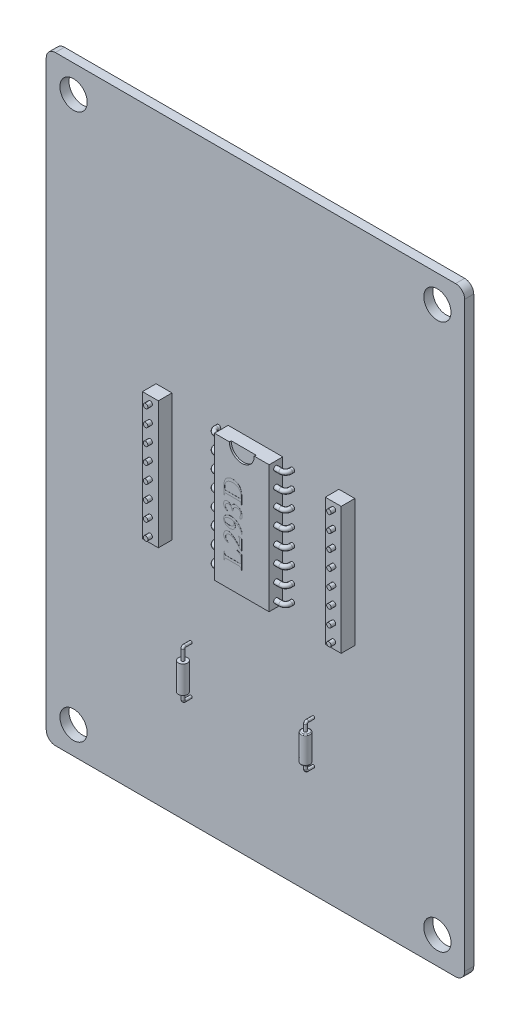
SolidWorks part; units mm, degrees
ref_plane "Plan de face" through (0, 0, 0) normal (0, 0, 1) x (1, 0, 0)
ref_plane "Plan de dessus" through (0, 0, 0) normal (0, 1, 0) x (1, 0, 0)
ref_plane "Plan de droite" through (0, 0, 0) normal (1, 0, 0) x (0, 0, -1)
sketch "Esquisse1" plane through (0, 0, 0) normal (0, 0, 1) x (1, 0, 0)
  line L6 (-23, 33) -> (-23, -33)
  line L7 (-23, -33) -> (23, -33)
  line L8 (23, 33) -> (23, -33)
  line L9 (-23, 33) -> (23, 33)
  circle A0 centre (-20, 30) radius 1.5
  circle A1 centre (20, 30) radius 1.5
  circle A2 centre (20, -30) radius 1.5
  circle A3 centre (-20, -30) radius 1.5
extrude "Boss.-Extru.1" add sketch "Esquisse1" along normal blind 1
fillet "Congé1" radius 1 4 edges at (23, -33, 0.5) (23, 33, 0.5) (-23, 33, 0.5) (-23, -33, 0.5)
sketch "Esquisse2" plane through (0, 0, 1) normal (0, 0, 1) x (1, 0, 0)
  line L2 (-3, 7) -> (3, 7)
  line L3 (3, 7) -> (3, -7)
  line L4 (-3, 7) -> (-3, -7)
  line L5 (-3, -7) -> (3, -7)
extrude "Boss.-Extru.2" add sketch "Esquisse2" along normal blind 1.5
sketch "Esquisse3" plane through (3, 0, 0) normal (1, 0, 0) x (0, 0, -1)
  circle A0 centre (-1.75, 0.9) radius 0.25
  dimension "D1" = 0.5
sketch3d "Esquisse3D1"
  line L0 (3, 0.9, 1.75) -> (3.5632, 0.9, 1.75)
  line L1 (4.0632, 0.9, 1.25) -> (4.0632, 0.9, 0.6073)
  arc A0 (3.5632, 0.9, 1.75) -> (4.0632, 0.9, 1.25) centre (3.5632, 0.9, 1.25) ccw
  point P7 (4.0632, 0.9, 1.75)
  point P8 (3.5632, 1.4, 1.25)
  dimension "D1" = 0.5
sweep "Balayage1" add profiles "Esquisse3" path "Esquisse3D1"
pattern_linear "Répétition linéaire1" count 4 spacing 1.8 along (0, 1, 0) of "Balayage1"
mirror "Symétrie1" about plane through (0, 0, 0) normal (0, 1, 0) of "Répétition linéaire1", "Balayage1"
mirror "Symétrie2" about plane through (0, 0, 0) normal (1, 0, 0) of "Symétrie1", "Balayage1", "Répétition linéaire1"
sketch "Esquisse4" plane through (0, 0, 2.5) normal (0, 0, 1) x (1, 0, 0)
  line L0 (3, 7) -> (-3, 7) construction
  line L1 (-1.3668, 7) -> (1.3668, 7)
  arc A0 (-1.3668, 7) -> (1.3668, 7) centre (0, 7) ccw
extrude "Enlèv. mat.-Extru.1" cut sketch "Esquisse4" against normal blind 0.2
sketch "Esquisse7" plane through (0, 0, 2.5) normal (0, 0, 1) x (1, 0, 0)
  line L0 (0, 20.7797) -> (0, -18.942) construction
  line L1 (-9.1755, 7) -> (-10.9232, 7)
  line L2 (-9.1755, 7) -> (-9.1755, -7)
  line L3 (-9.1755, -7) -> (-10.9232, -7)
  line L4 (-10.9232, 7) -> (-10.9232, -7)
  line L6 (10.9232, 7) -> (10.9232, -7)
  line L7 (9.1755, -7) -> (10.9232, -7)
  line L8 (9.1755, 7) -> (9.1755, -7)
  line L9 (9.1755, 7) -> (10.9232, 7)
extrude "Boss.-Extru.6" add sketch "Esquisse7" against normal blind 1.5 separate body
sketch "Esquisse8" plane through (0, 0, 1) normal (0, 0, -1) x (-1, 0, 0)
  line L0 (0, 14.1831) -> (0, -11.9135) construction
  circle A0 centre (-10.0843, 0.9) radius 0.25
  circle A1 centre (-10.0806, 2.7) radius 0.25
  circle A2 centre (-10.077, 4.5) radius 0.25
  circle A3 centre (-10.0733, 6.3) radius 0.25
  circle A4 centre (-10.0733, -6.3) radius 0.25
  circle A5 centre (-10.077, -4.5) radius 0.25
  circle A6 centre (-10.0806, -2.7) radius 0.25
  circle A7 centre (-10.0843, -0.9) radius 0.25
  circle A8 centre (10.0843, -0.9) radius 0.25
  circle A9 centre (10.0806, -2.7) radius 0.25
  circle A10 centre (10.077, -4.5) radius 0.25
  circle A11 centre (10.0733, -6.3) radius 0.25
  circle A12 centre (10.0733, 6.3) radius 0.25
  circle A13 centre (10.077, 4.5) radius 0.25
  circle A14 centre (10.0806, 2.7) radius 0.25
  circle A15 centre (10.0843, 0.9) radius 0.25
  dimension "D2" = 0.5
  dimension "D3" = 4
extrude "Boss.-Extru.7" add sketch "Esquisse8" against normal blind 2
sketch "Esquisse9" plane through (0, 0, 0) normal (0, 1, 0) x (1, 0, 0)
  circle A0 centre (6.3665, -1.8577) radius 0.5
  circle A1 centre (-7.1104, -1.8577) radius 0.5
  dimension "D1" = 1
  dimension "D2" = 1
extrude "Boss.-Extru.8" add sketch "Esquisse9" along normal blind 3 from offset 20 separate body offset against normal yes
sketch "Esquisse10" plane through (0, -20, 0) normal (0, -1, 0) x (1, 0, 0)
  circle A2 centre (6.3665, 1.8577) radius 0.15
  circle A3 centre (6.3665, 1.8577) radius 0.15
  dimension "D1" = 0.35
extrude "Boss.-Extru.9" add sketch "Esquisse10" against normal blind 4 from offset 0.5
sketch "Esquisse11" plane through (0, -20.5, 0) normal (0, -1, 0) x (1, 0, 0)
  circle A0 centre (6.3665, 1.8577) radius 0.15 construction
  circle A1 centre (6.3665, 1.8577) radius 0.15
sketch3d "Esquisse3D2"
  line L0 (6.3665, -20.5, 1.8577) -> (6.3665, -20.5934, 1.8577)
  line L1 (6.3665, -20.7634, 1.6877) -> (6.3665, -20.7634, 0.4823)
  arc A0 (6.3665, -20.5934, 1.8577) -> (6.3665, -20.7634, 1.6877) centre (6.3665, -20.5934, 1.6877) ccw
  point P7 (6.3665, -20.7634, 1.8577)
  point P8 (6.5365, -20.5934, 1.6877)
  dimension "D1" = 0.17
sweep "Balayage2" add profiles "Esquisse11" path "Esquisse3D2"
sketch "Esquisse12" plane through (0, -16.5, 0) normal (0, 1, 0) x (1, 0, 0)
  circle A0 centre (6.3665, -1.8577) radius 0.15 construction
  circle A1 centre (6.3665, -1.8577) radius 0.15
sketch3d "Esquisse3D3"
  line L0 (6.3665, -16.5, 1.8577) -> (6.3665, -16.2882, 1.8577)
  line L1 (6.3665, -16.1182, 1.6877) -> (6.3665, -16.1182, 0.8386)
  arc A0 (6.3665, -16.2882, 1.8577) -> (6.3665, -16.1182, 1.6877) centre (6.3665, -16.2882, 1.6877) ccw
  point P6 (6.3665, -16.1182, 1.8577)
  point P7 (6.1965, -16.2882, 1.6877)
  dimension "D1" = 0.17
sweep "Balayage3" add profiles "Esquisse12" path "Esquisse3D3"
fillet "Congé2" radius 0.1 2 edges at (6.3665, -20, 2.3577) (6.3665, -17, 2.3577)
sketch "Esquisse13" plane through (0, -20, 0) normal (0, -1, 0) x (1, 0, 0)
  circle A1 centre (-7.1104, 1.8577) radius 0.15
  dimension "D1" = 0.3
sketch3d "Esquisse3D4"
  line L0 (-7.1104, -20, 1.8577) -> (-7.1104, -20.7212, 1.8577)
  line L1 (-7.1104, -20.8912, 1.6877) -> (-7.1104, -20.8912, 0.5371)
  arc A0 (-7.1104, -20.7212, 1.8577) -> (-7.1104, -20.8912, 1.6877) centre (-7.1104, -20.7212, 1.6877) ccw
  point P6 (-7.1104, -20.8912, 1.8577)
  point P7 (-6.9404, -20.7212, 1.6877)
  dimension "D1" = 0.17
sweep "Balayage4" add profiles "Esquisse13" path "Esquisse3D4"
sketch "Esquisse14" plane through (0, -17, 0) normal (0, 1, 0) x (1, 0, 0)
  circle A2 centre (-7.1104, -1.8577) radius 0.15
  circle A3 centre (-7.1104, -1.8577) radius 0.15
  dimension "D1" = 0.35
sketch3d "Esquisse3D5"
  line L0 (-7.1104, -17, 1.8577) -> (-7.1104, -15.8613, 1.8577)
  line L1 (-7.1104, -15.6913, 1.6877) -> (-7.1104, -15.6913, 0.5641)
  arc A0 (-7.1104, -15.8613, 1.8577) -> (-7.1104, -15.6913, 1.6877) centre (-7.1104, -15.8613, 1.6877) ccw
  point P6 (-7.1104, -15.6913, 1.8577)
  point P7 (-7.2804, -15.8613, 1.6877)
  dimension "D1" = 0.17
sweep "Balayage5" add profiles "Esquisse14" path "Esquisse3D5"
sketch "Esquisse15" plane through (0, 0, 2.5) normal (0, 0, 1) x (1, 0, 0)
  line L0 (0, 5.1335) -> (0, -5.9621) construction
  text T0 "L293D" font "Times New Roman" height in points 8
extrude "Boss.-Extru.10" add sketch "Esquisse15" along normal blind 0.01
